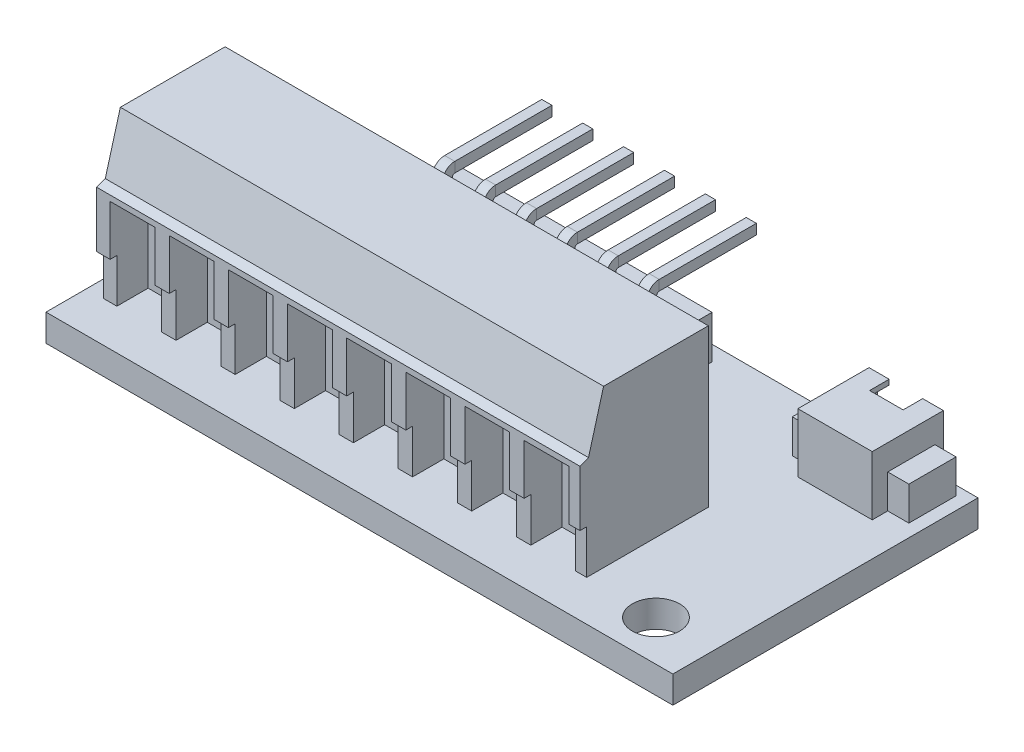
SolidWorks part; units mm, degrees
ref_plane "Front Plane" through (0, 0, 0) normal (0, 0, 1) x (1, 0, 0)
ref_plane "Top Plane" through (0, 0, 0) normal (0, 1, 0) x (1, 0, 0)
ref_plane "Right Plane" through (0, 0, 0) normal (1, 0, 0) x (0, 0, -1)
sketch "Sketch1" plane through (0, 0, 0) normal (0, 1, 0) x (1, 0, 0)
  line L1 (0, 0) -> (37.1, 0)
  line L2 (0, 0) -> (0, 18.06)
  line L3 (0, 18.06) -> (37.1, 18.06)
  line L4 (37.1, 0) -> (37.1, 18.06)
  circle A0 centre (33.7, 2.4) radius 1.4
  circle A1 centre (2.8, 14.16) radius 1.4
  dimension "D3" = 2.8
  dimension "D4" = 2.8
  dimension "D1" = 37.1
  dimension "D2" = 18.06
  dimension "D5" = 3.4
  dimension "D6" = 2.4
  dimension "D7" = 3.9
  dimension "D8" = 2.8
extrude "Boss-Extrude1" add sketch "Sketch1" along normal blind 1.6
sketch "Sketch2" plane through (0, 1.6, 0) normal (0, 1, 0) x (1, 0, 0)
  line L0 (37.1, 18.06) -> (0, 18.06) construction
  line L1 (7.0602, 17.16) -> (22.2602, 17.16)
  line L2 (7.0602, 17.16) -> (7.0602, 15.56)
  line L3 (7.0602, 12.46) -> (22.2602, 12.46)
  line L4 (22.2602, 17.16) -> (22.2602, 15.56)
  line L5 (10.1802, 15.56) -> (10.1802, 14.06)
  line L6 (7.0602, 15.56) -> (7.7602, 15.56)
  line L8 (7.0602, 14.06) -> (7.7602, 14.06)
  line L9 (7.7602, 15.56) -> (7.7602, 14.06)
  line L10 (9.4802, 15.56) -> (10.1802, 15.56)
  line L11 (9.4802, 14.06) -> (10.1802, 14.06)
  line L12 (9.4802, 15.56) -> (9.4802, 14.06)
  line L13 (12.6002, 15.56) -> (12.6002, 14.06)
  line L14 (11.9002, 15.56) -> (12.6002, 15.56)
  line L15 (11.9002, 14.06) -> (12.6002, 14.06)
  line L16 (11.9002, 15.56) -> (11.9002, 14.06)
  line L17 (15.0202, 15.56) -> (15.0202, 14.06)
  line L18 (14.3202, 15.56) -> (15.0202, 15.56)
  line L19 (14.3202, 14.06) -> (15.0202, 14.06)
  line L20 (14.3202, 15.56) -> (14.3202, 14.06)
  line L21 (17.4402, 15.56) -> (17.4402, 14.06)
  line L22 (16.7402, 15.56) -> (17.4402, 15.56)
  line L23 (16.7402, 14.06) -> (17.4402, 14.06)
  line L24 (16.7402, 15.56) -> (16.7402, 14.06)
  line L25 (19.8602, 15.56) -> (19.8602, 14.06)
  line L26 (19.1602, 15.56) -> (19.8602, 15.56)
  line L27 (19.1602, 14.06) -> (19.8602, 14.06)
  line L28 (19.1602, 15.56) -> (19.1602, 14.06)
  line L30 (21.5802, 15.56) -> (22.2602, 15.56)
  line L31 (21.5802, 14.06) -> (22.2602, 14.06)
  line L32 (21.5802, 15.56) -> (21.5802, 14.06)
  line L33 (22.2802, 15.56) -> (22.2802, 14.06) [skipped]
  line L34 (7.0602, 14.06) -> (7.0602, 12.46)
  line L35 (22.2602, 14.06) -> (22.2602, 12.46)
  dimension "D1" = 0.9
  dimension "D2" = 15.2
  dimension "D3" = 4.7
  dimension "D4" = 1.5
  dimension "D6" = 0.7
  dimension "D7" = 7
extrude "Boss-Extrude2" add sketch "Sketch2" along normal blind 2.54
ref_plane "Plane1" through (8.6102, 0, 0) normal (-1, 0, 0) x (0, 0, 1)
sketch "Sketch3" plane through (8.6102, 0, 0) normal (-1, 0, 0) x (0, 0, 1)
  line L0 (-14.5331, 4.14) -> (-14.5331, 5.39)
  line L1 (-15.56, 4.14) -> (-14.06, 4.14) construction
  line L2 (-15.2831, 6.14) -> (-21.0331, 6.14)
  arc A0 (-14.5331, 5.39) -> (-15.2831, 6.14) centre (-15.2831, 5.39) ccw
  point P7 (-14.5331, 6.14)
  dimension "D2" = 0.75
  dimension "D1" = 2
sketch "Sketch4" plane through (0, 4.14, 0) normal (0, 1, 0) x (1, 0, 0)
  line L0 (8.6102, 0.825) -> (8.6102, -0.825) construction
  line L1 (8.9102, 15.1331) -> (8.3102, 15.1331)
  line L2 (8.9102, 15.1331) -> (8.9102, 14.5331)
  line L3 (8.9102, 14.5331) -> (8.3102, 14.5331)
  line L4 (8.3102, 15.1331) -> (8.3102, 14.5331)
  dimension "D1" = 0.6
  dimension "D2" = 0.6
  dimension "D3" = 0.3
  dimension "D4" = 0
sweep "Sweep1" add profiles "Sketch4" path "Sketch3"
pattern_linear "LPattern1" count 6 spacing 2.42 along (1, 0, 0) of "Sweep1"
sketch "Sketch6" plane through (0, 1.6, 0) normal (0, 1, 0) x (1, 0, 0)
  line L0 (0, 18.06) -> (0, 0) construction
  line L1 (1, 2) -> (29.6, 2)
  line L2 (1, 2) -> (1, 9.6)
  line L3 (1, 9.6) -> (29.6, 9.6)
  line L4 (29.6, 2) -> (29.6, 9.6)
  line L5 (0, 0) -> (37.1, 0) construction
  dimension "D1" = 7.6
  dimension "D2" = 28.6
  dimension "D3" = 1
  dimension "D4" = 2
extrude "Boss-Extrude3" add sketch "Sketch6" along normal blind 9.3
sketch "Sketch7" plane through (1, 0, 0) normal (-1, 0, 0) x (0, 0, 1)
  line L0 (-2, 7.5) -> (-2.5081, 7.6887)
  line L1 (-2, 1.6) -> (-2.4, 1.6)
  line L2 (-2, 1.6) -> (-2, 4.2)
  line L3 (-2, 4.2) -> (-2.4, 4.2)
  line L4 (-2.4, 1.6) -> (-2.4, 4.2)
  line L5 (-2, 10.9) -> (-2, 1.6) construction
  line L6 (-2.5081, 7.6887) -> (-3.4, 10.9)
  line L7 (-9.6, 10.9) -> (-2, 10.9) construction
  line L8 (-3.4, 10.9) -> (-2, 10.9)
  line L9 (-2, 10.9) -> (-2, 7.5)
  dimension "D1" = 0.4
  dimension "D2" = 2.6
  dimension "D3" = 3.3
  dimension "D4" = 1.4
extrude "Cut-Extrude1" cut sketch "Sketch7" against normal up to next
sketch "Sketch8" plane through (0, 0, -2) normal (0, 0, 1) x (1, 0, 0)
  line L0 (0, 1.6) -> (37.1, 1.6) construction
  line L1 (1.7955, 7.1717) -> (4.4455, 7.1717)
  line L2 (1.7955, 7.1717) -> (1.7955, 1.6)
  line L3 (1.7955, 1.6) -> (4.4455, 1.6)
  line L4 (4.4455, 7.1717) -> (4.4455, 1.6)
  line L5 (5.2955, 7.1717) -> (5.2955, 1.6)
  line L6 (5.2955, 1.6) -> (7.9455, 1.6)
  line L7 (7.9455, 7.1717) -> (7.9455, 1.6)
  line L8 (5.2955, 7.1717) -> (7.9455, 7.1717)
  line L9 (8.7955, 7.1717) -> (8.7955, 1.6)
  line L10 (8.7955, 1.6) -> (11.4455, 1.6)
  line L11 (11.4455, 7.1717) -> (11.4455, 1.6)
  line L12 (8.7955, 7.1717) -> (11.4455, 7.1717)
  line L13 (12.2955, 7.1717) -> (12.2955, 1.6)
  line L14 (12.2955, 1.6) -> (14.9455, 1.6)
  line L15 (14.9455, 7.1717) -> (14.9455, 1.6)
  line L16 (12.2955, 7.1717) -> (14.9455, 7.1717)
  line L17 (15.7955, 7.1717) -> (15.7955, 1.6)
  line L18 (15.7955, 1.6) -> (18.4455, 1.6)
  line L19 (18.4455, 7.1717) -> (18.4455, 1.6)
  line L20 (15.7955, 7.1717) -> (18.4455, 7.1717)
  line L21 (19.2955, 7.1717) -> (19.2955, 1.6)
  line L22 (19.2955, 1.6) -> (21.9455, 1.6)
  line L23 (21.9455, 7.1717) -> (21.9455, 1.6)
  line L24 (19.2955, 7.1717) -> (21.9455, 7.1717)
  line L25 (22.7955, 7.1717) -> (22.7955, 1.6)
  line L26 (22.7955, 1.6) -> (25.4455, 1.6)
  line L27 (25.4455, 7.1717) -> (25.4455, 1.6)
  line L28 (22.7955, 7.1717) -> (25.4455, 7.1717)
  line L29 (26.2955, 7.1717) -> (26.2955, 1.6)
  line L30 (26.2955, 1.6) -> (28.9455, 1.6)
  line L31 (28.9455, 7.1717) -> (28.9455, 1.6)
  line L32 (26.2955, 7.1717) -> (28.9455, 7.1717)
  dimension "D1" = 2.65
  dimension "D2" = 8
extrude "Cut-Extrude2" cut sketch "Sketch8" against normal blind 2.25
sketch "Sketch9" plane through (0, 1.6, 0) normal (0, 1, 0) x (1, 0, 0)
  line L0 (37.1, 18.06) -> (0, 18.06) construction
  line L1 (30.7, 18.01) -> (35.1, 18.01)
  line L2 (30.7, 18.01) -> (30.7, 13.8)
  line L3 (30.7, 13.8) -> (35.1, 13.8)
  line L4 (35.1, 18.01) -> (35.1, 13.8)
  line L5 (37.1, 0) -> (37.1, 18.06) construction
  dimension "D1" = 4.4
  dimension "D2" = 0.05
  dimension "D3" = 4.21
  dimension "D4" = 2
extrude "Boss-Extrude4" add sketch "Sketch9" along normal blind 3.5
sketch "Sketch10" plane through (0, 1.6, 0) normal (0, 1, 0) x (1, 0, 0)
  line L0 (35.1, 13.8) -> (35.1, 18.01) construction
  line L1 (29.45, 17.51) -> (36.35, 17.51)
  line L2 (29.45, 17.51) -> (29.45, 14.7177)
  line L3 (29.45, 14.7177) -> (36.35, 14.7177)
  line L4 (36.35, 17.51) -> (36.35, 14.7177)
  line L5 (30.7, 18.01) -> (30.7, 13.8) construction
  line L6 (35.1, 18.01) -> (30.7, 18.01) construction
  dimension "D1" = 1.25
  dimension "D2" = 1.25
  dimension "D3" = 0.5
extrude "Boss-Extrude5" add sketch "Sketch10" along normal blind 2 contours L3 L4 L1 L2
sketch "Sketch11" plane through (0, 0, -18.01) normal (0, 0, -1) x (-1, 0, 0)
  line L0 (-35.1, 5.1) -> (-30.7, 5.1) construction
  line L1 (-31.202, 2.1) -> (-34.502, 2.1)
  line L2 (-31.202, 2.1) -> (-31.202, 4.8)
  line L3 (-31.202, 4.8) -> (-34.502, 4.8)
  line L4 (-34.502, 2.1) -> (-34.502, 4.8)
  line L5 (-37.1, 1.6) -> (0, 1.6) construction
  dimension "D1" = 0.3
  dimension "D2" = 3.3
  dimension "D3" = 0.5
extrude "Cut-Extrude3" cut sketch "Sketch11" against normal blind 3.5
sketch "Sketch12" plane through (0, 5.1, 0) normal (0, 1, 0) x (1, 0, 0)
  line L0 (35.1, 18.01) -> (30.7, 18.01) construction
  line L1 (31.8912, 18.01) -> (33.8764, 18.01)
  line L2 (31.8912, 18.01) -> (31.8912, 16.853)
  line L3 (31.8912, 16.853) -> (33.8764, 16.853)
  line L4 (33.8764, 18.01) -> (33.8764, 16.853)
extrude "Cut-Extrude4" cut sketch "Sketch12" against normal up to next
